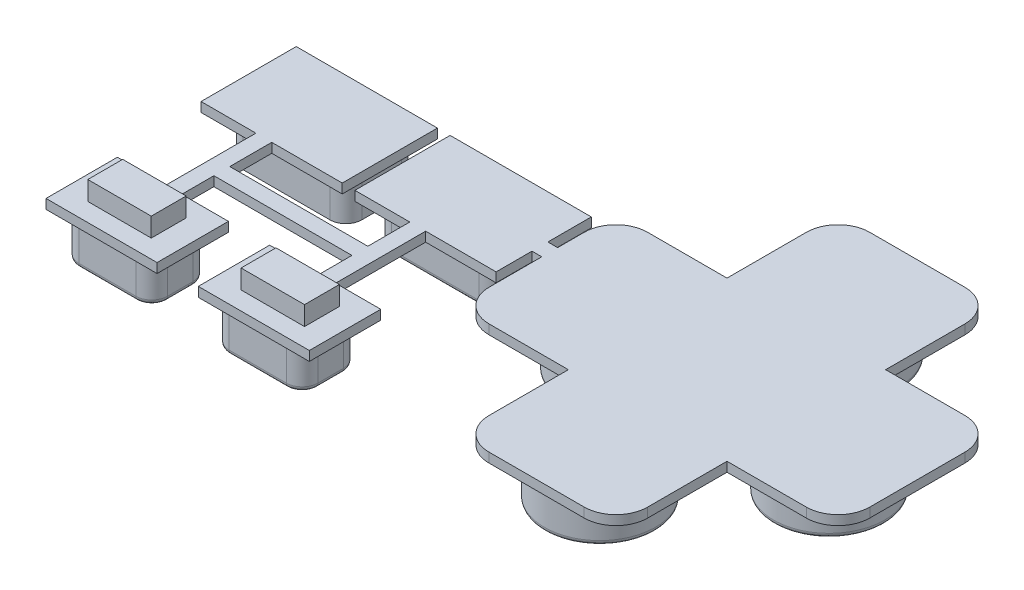
SolidWorks part; units mm, degrees
ref_plane "前视基准面" through (0, 0, 0) normal (0, 0, 1) x (1, 0, 0)
ref_plane "上视基准面" through (0, 0, 0) normal (0, 1, 0) x (1, 0, 0)
ref_plane "右视基准面" through (0, 0, 0) normal (1, 0, 0) x (0, 0, -1)
sketch "草图1" plane through (0, 0, 0) normal (0, 1, 0) x (1, 0, 0)
  line L32 (-10.3556, -1.581) -> (-15.3556, -1.581)
  line L33 (-10.3556, -6.581) -> (-10.3556, -1.581)
  line L34 (-2.3556, -8.581) -> (-8.3556, -8.581)
  line L35 (-0.3556, -1.581) -> (-0.3556, -6.581)
  line L36 (4.6444, -1.581) -> (-0.3556, -1.581)
  line L37 (6.6444, 6.419) -> (6.6444, 0.419)
  line L38 (-0.3556, 8.419) -> (4.6444, 8.419)
  line L39 (-0.3556, 13.419) -> (-0.3556, 8.419)
  line L40 (-8.3556, 15.419) -> (-2.3556, 15.419)
  line L41 (-10.3556, 8.419) -> (-10.3556, 13.419)
  line L42 (-15.3556, 8.419) -> (-10.3556, 8.419)
  line L43 (-17.3556, 0.419) -> (-17.3556, 6.419)
  arc A24 (-17.3556, 0.419) -> (-15.3556, -1.581) centre (-15.3556, 0.419) ccw
  arc A26 (-10.3556, -6.581) -> (-8.3556, -8.581) centre (-8.3556, -6.581) ccw
  arc A27 (-2.3556, -8.581) -> (-0.3556, -6.581) centre (-2.3556, -6.581) ccw
  arc A29 (4.6444, -1.581) -> (6.6444, 0.419) centre (4.6444, 0.419) ccw
  arc A30 (6.6444, 6.419) -> (4.6444, 8.419) centre (4.6444, 6.419) ccw
  arc A32 (-0.3556, 13.419) -> (-2.3556, 15.419) centre (-2.3556, 13.419) ccw
  arc A33 (-8.3556, 15.419) -> (-10.3556, 13.419) centre (-8.3556, 13.419) ccw
  arc A35 (-15.3556, 8.419) -> (-17.3556, 6.419) centre (-15.3556, 6.419) ccw
extrude "凸台-拉伸1" add sketch "草图1" along normal blind 0.6
sketch "草图2" plane through (0, 0, 0) normal (0, -1, 0) x (1, 0, 0)
  line L24 (-15.7556, -0.419) -> (-15.7556, -6.419)
  line L25 (-15.3556, -6.819) -> (-8.7556, -6.819)
  line L26 (-8.7556, -6.819) -> (-8.7556, -13.419)
  line L27 (-8.3556, -13.819) -> (-2.3556, -13.819)
  line L28 (-1.9556, -13.419) -> (-1.9556, -6.819)
  line L29 (-1.9556, -6.819) -> (4.6444, -6.819)
  line L30 (5.0444, -6.419) -> (5.0444, -0.419)
  line L31 (4.6444, -0.019) -> (-1.9556, -0.019)
  line L32 (-1.9556, -0.019) -> (-1.9556, 6.581)
  line L33 (-2.3556, 6.981) -> (-8.3556, 6.981)
  line L34 (-8.7556, 6.581) -> (-8.7556, -0.019)
  line L35 (-8.7556, -0.019) -> (-15.3556, -0.019)
  line L36 (-15.7556, -0.419) -> (-15.7556, -6.419)
  line L37 (-15.3556, -6.819) -> (-8.7556, -6.819)
  line L38 (-8.7556, -6.819) -> (-8.7556, -13.419)
  line L39 (-8.3556, -13.819) -> (-2.3556, -13.819)
  line L40 (-1.9556, -13.419) -> (-1.9556, -6.819)
  line L41 (-1.9556, -6.819) -> (4.6444, -6.819)
  line L42 (5.0444, -6.419) -> (5.0444, -0.419)
  line L43 (4.6444, -0.019) -> (-1.9556, -0.019)
  line L44 (-1.9556, -0.019) -> (-1.9556, 6.581)
  line L45 (-2.3556, 6.981) -> (-8.3556, 6.981)
  line L46 (-8.7556, 6.581) -> (-8.7556, -0.019)
  line L47 (-8.7556, -0.019) -> (-15.3556, -0.019)
  arc A16 (-15.3556, -0.019) -> (-15.7556, -0.419) centre (-15.3556, -0.419) ccw
  arc A17 (-15.7556, -6.419) -> (-15.3556, -6.819) centre (-15.3556, -6.419) ccw
  arc A18 (-8.7556, -13.419) -> (-8.3556, -13.819) centre (-8.3556, -13.419) ccw
  arc A19 (-2.3556, -13.819) -> (-1.9556, -13.419) centre (-2.3556, -13.419) ccw
  arc A20 (4.6444, -6.819) -> (5.0444, -6.419) centre (4.6444, -6.419) ccw
  arc A21 (5.0444, -0.419) -> (4.6444, -0.019) centre (4.6444, -0.419) ccw
  arc A22 (-1.9556, 6.581) -> (-2.3556, 6.981) centre (-2.3556, 6.581) ccw
  arc A23 (-8.3556, 6.981) -> (-8.7556, 6.581) centre (-8.3556, 6.581) ccw
  arc A24 (-15.3556, -0.019) -> (-15.7556, -0.419) centre (-15.3556, -0.419) ccw
  arc A25 (-15.7556, -6.419) -> (-15.3556, -6.819) centre (-15.3556, -6.419) ccw
  arc A26 (-8.7556, -13.419) -> (-8.3556, -13.819) centre (-8.3556, -13.419) ccw
  arc A27 (-2.3556, -13.819) -> (-1.9556, -13.419) centre (-2.3556, -13.419) ccw
  arc A28 (4.6444, -6.819) -> (5.0444, -6.419) centre (4.6444, -6.419) ccw
  arc A29 (5.0444, -0.419) -> (4.6444, -0.019) centre (4.6444, -0.419) ccw
  arc A30 (-1.9556, 6.581) -> (-2.3556, 6.981) centre (-2.3556, 6.581) ccw
  arc A31 (-8.3556, 6.981) -> (-8.7556, 6.581) centre (-8.3556, 6.581) ccw
  dimension "D1" = 1.6
sketch "草图3" plane through (0, 0, 0) normal (0, -1, 0) x (1, 0, 0)
  line L0 (-10.3556, 1.581) -> (-10.3556, 6.581) construction
  line L1 (-36.573, -1.4829) -> (-27.673, -1.4829)
  line L2 (-36.573, -1.4829) -> (-36.573, -7.4829)
  line L3 (-36.573, -7.4829) -> (-27.673, -7.4829)
  line L4 (-27.673, -1.4829) -> (-27.673, -7.4829)
  line L5 (-26.873, -1.4829) -> (-17.973, -1.4829)
  line L6 (-26.873, -1.4829) -> (-26.873, -7.4829)
  line L7 (-26.873, -7.4829) -> (-17.973, -7.4829)
  line L8 (-17.973, -1.4829) -> (-17.973, -7.4829)
  line L9 (-36.1688, 8.696) -> (-29.1688, 8.696)
  line L10 (-36.1688, 8.696) -> (-36.1688, 4.196)
  line L11 (-36.1688, 4.196) -> (-29.1688, 4.196)
  line L12 (-29.1688, 8.696) -> (-29.1688, 4.196)
  line L13 (-26.5688, 8.696) -> (-19.5688, 8.696)
  line L14 (-26.5688, 8.696) -> (-26.5688, 4.196)
  line L15 (-26.5688, 4.196) -> (-19.5688, 4.196)
  line L16 (-19.5688, 8.696) -> (-19.5688, 4.196)
  line L17 (-15.3556, 1.581) -> (-10.3556, 1.581) construction
  line L18 (-17.3556, -6.419) -> (-17.3556, -0.419) construction
  line L19 (-10.3556, -8.419) -> (-15.3556, -8.419) construction
  dimension "D1" = 6
  dimension "D2" = 8.9
  dimension "D3" = 7
  dimension "D4" = 4.5
  dimension "D5" = 2.6
  dimension "D6" = 0.8
  dimension "D7" = 9.2131
  dimension "D8" = 2.615
  dimension "D9" = 0.6174
  dimension "D10" = 0.936
extrude "凸台-拉伸3" add sketch "草图3" against normal blind 0.6 separate body
sketch "草图4" plane through (0, 0, 0) normal (0, -1, 0) x (1, 0, 0)
  line L1 (-33.1166, 4.7185) -> (-32.1166, 4.7185)
  line L2 (-33.1166, 4.7185) -> (-33.1166, -1.6561)
  line L3 (-33.1166, -1.6561) -> (-32.1166, -1.6561)
  line L4 (-32.1166, 4.7185) -> (-32.1166, -1.6561)
  line L7 (-23.4153, 4.8891) -> (-22.4153, 4.8891)
  line L8 (-23.4153, 4.8891) -> (-23.4153, -1.7621)
  line L9 (-23.4153, -1.7621) -> (-22.4153, -1.7621)
  line L10 (-22.4153, 4.8891) -> (-22.4153, -1.7621)
  dimension "D1" = 1
  dimension "D2" = 1
extrude "凸台-拉伸4" add sketch "草图4" against normal blind 0.6 separate body
sketch "草图5" plane through (0, 0, 0) normal (0, -1, 0) x (1, 0, 0)
  line L0 (-32.1166, -1.6561) -> (-32.1166, 4.7185) construction
  line L1 (-32.1166, 2.1635) -> (-23.4153, 2.1635)
  line L2 (-32.1166, 2.1635) -> (-32.1166, 1.1635)
  line L3 (-32.1166, 1.1635) -> (-23.4153, 1.1635)
  line L4 (-23.4153, 2.1635) -> (-23.4153, 1.1635)
  line L5 (-23.4153, 4.8891) -> (-23.4153, -1.7621) construction
  line L6 (-17.973, -7.4829) -> (-17.973, -1.4829) construction
  line L7 (-17.973, -3.7438) -> (-17.3556, -3.7438)
  line L8 (-17.973, -3.7438) -> (-17.973, -4.7438)
  line L9 (-17.973, -4.7438) -> (-17.3556, -4.7438)
  line L10 (-17.3556, -3.7438) -> (-17.3556, -4.7438)
  line L11 (-17.3556, -6.419) -> (-17.3556, -0.419) construction
  dimension "D1" = 1
  dimension "D2" = 1
extrude "凸台-拉伸5" add sketch "草图5" against normal blind 0.6
sketch "草图6" plane through (0, 0, 0) normal (0, -1, 0) x (1, 0, 0)
  line L0 (-36.1688, 8.696) -> (-36.1688, 4.196) construction
  line L1 (-35.4979, 8.3012) -> (-29.8979, 8.3012)
  line L2 (-35.4979, 8.3012) -> (-35.4979, 4.7012)
  line L3 (-35.4979, 4.7012) -> (-29.8979, 4.7012)
  line L4 (-29.8979, 8.3012) -> (-29.8979, 4.7012)
  line L5 (-26.0167, 8.3012) -> (-20.4167, 8.3012)
  line L6 (-26.0167, 8.3012) -> (-26.0167, 4.7012)
  line L7 (-26.0167, 4.7012) -> (-20.4167, 4.7012)
  line L8 (-20.4167, 8.3012) -> (-20.4167, 4.7012)
  line L9 (-29.1688, 8.696) -> (-36.1688, 8.696) construction
  line L10 (-26.5688, 8.696) -> (-26.5688, 4.196) construction
  line L11 (-27.673, -1.4829) -> (-36.573, -1.4829) construction
  line L12 (-35.743, -2.2829) -> (-28.243, -2.2829)
  line L13 (-35.743, -2.2829) -> (-35.743, -6.7829)
  line L14 (-35.743, -6.7829) -> (-28.243, -6.7829)
  line L15 (-28.243, -2.2829) -> (-28.243, -6.7829)
  line L16 (-26.363, -2.2829) -> (-18.863, -2.2829)
  line L17 (-26.363, -2.2829) -> (-26.363, -6.7829)
  line L18 (-26.363, -6.7829) -> (-18.863, -6.7829)
  line L19 (-18.863, -2.2829) -> (-18.863, -6.7829)
  line L20 (-36.573, -1.4829) -> (-36.573, -7.4829) construction
  dimension "D1" = 5.6
  dimension "D2" = 0.6709
  dimension "D3" = 3.6
  dimension "D4" = 0.3948
  dimension "D5" = 0.552
  dimension "D6" = 7.5
  dimension "D7" = 4.5
  dimension "D8" = 0.8
  dimension "D9" = 0.83
  dimension "D10" = 1.88
extrude "凸台-拉伸6" add sketch "草图6" along normal blind 2.6
fillet "圆角2" radius 1 16 edges at (-26.363, -1.3, -6.7829) (-18.863, -1.3, -6.7829) (-18.863, -1.3, -2.2829) (-26.363, -1.3, -2.2829) (-28.243, -1.3, -2.2829) (-35.743, -1.3, -2.2829) (-35.743, -1.3, -6.7829) (-28.243, -1.3, -6.7829) (-20.4167, -1.3, 4.7012) (-26.0167, -1.3, 4.7012) (-20.4167, -1.3, 8.3012) (-26.0167, -1.3, 8.3012) (-35.4979, -1.3, 8.3012) (-29.8979, -1.3, 8.3012) (-29.8979, -1.3, 4.7012) (-35.4979, -1.3, 4.7012)
sketch "草图8" plane through (0, 0.6, 0) normal (0, 1, 0) x (1, 0, 0)
  line L1 (-34.6856, -5.3444) -> (-30.6856, -5.3444)
  line L2 (-34.6856, -5.3444) -> (-34.6856, -7.5444)
  line L3 (-34.6856, -7.5444) -> (-30.6856, -7.5444)
  line L4 (-30.6856, -5.3444) -> (-30.6856, -7.5444)
  line L5 (-34.6856, -5.3444) -> (-30.6856, -7.5444) construction
  line L6 (-34.6856, -7.5444) -> (-30.6856, -5.3444) construction
  line L7 (-25.0234, -5.3444) -> (-21.0234, -5.3444)
  line L8 (-25.0234, -5.3444) -> (-25.0234, -7.5444)
  line L9 (-25.0234, -7.5444) -> (-21.0234, -7.5444)
  line L10 (-21.0234, -5.3444) -> (-21.0234, -7.5444)
  line L11 (-25.0234, -5.3444) -> (-21.0234, -7.5444) construction
  line L12 (-25.0234, -7.5444) -> (-21.0234, -5.3444) construction
  point P0 (-32.6856, -6.4444)
  point P5 (-23.0234, -6.4444)
  dimension "D1" = 4
  dimension "D2" = 2.2
extrude "凸台-拉伸7" add sketch "草图8" along normal blind 1.2
sketch "草图9" plane through (0, 0, 0) normal (0, -1, 0) x (1, 0, 0)
  circle A0 centre (-12.0244, -3.2762) radius 3.5
  circle A1 centre (-5.6044, 4.3438) radius 3.5
  circle A2 centre (-5.6044, -11.069) radius 3.5
  circle A3 centre (1.2256, -3.2762) radius 3.5
  dimension "D1" = 7
extrude "凸台-拉伸8" add sketch "草图9" along normal blind 2.8
fillet "圆角3" radius 0.3 4 edges at (-5.6044, -2.8, -14.569) (-12.0244, -2.8, -6.7762) (1.2256, -2.8, -6.7762) (-5.6044, -2.8, 0.8438)
fillet "圆角4" radius 0.3 32 edges at (-28.5359, 0, -2.5758) (-28.243, 0, -4.5329) (-28.5359, 0, -6.4901) (-31.993, 0, -6.7829) (-35.4501, 0, -6.4901) (-35.743, 0, -4.5329) (-35.4501, 0, -2.5758) (-25.7238, -2.6, 4.9941) (-26.0167, -2.6, 6.5012) (-25.7238, -2.6, 8.0083) (-23.2167, -2.6, 8.3012) (-20.7096, -2.6, 8.0083) (-20.4167, -2.6, 6.5012) (-20.7096, -2.6, 4.9941) (-23.2167, -2.6, 4.7012) (-30.1908, -2.6, 8.0083) (-29.8979, -2.6, 6.5012) (-30.1908, -2.6, 4.9941) (-32.6979, -2.6, 4.7012) (-35.205, -2.6, 4.9941) (-35.4979, -2.6, 6.5012) (-35.205, -2.6, 8.0083) (-32.6979, -2.6, 8.3012) (-26.0701, -2.6, -2.5758) (-22.613, -2.6, -2.2829) (-19.1559, -2.6, -2.5758) (-18.863, -2.6, -4.5329) (-19.1559, -2.6, -6.4901) (-22.613, -2.6, -6.7829) (-26.0701, -2.6, -6.4901) (-26.363, -2.6, -4.5329) (-31.993, 0, -2.2829)
